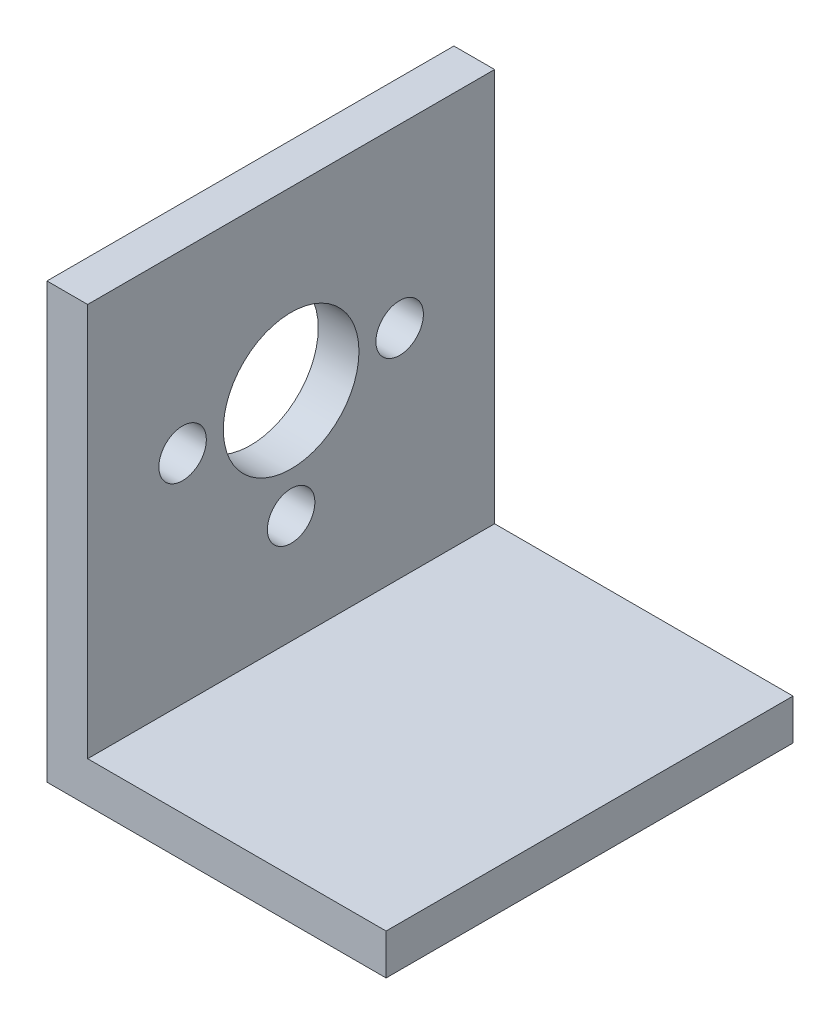
SolidWorks part; units mm, degrees
ref_plane "Front Plane" through (0, 0, 0) normal (0, 0, 1) x (1, 0, 0)
ref_plane "Top Plane" through (0, 0, 0) normal (0, 1, 0) x (1, 0, 0)
ref_plane "Right Plane" through (0, 0, 0) normal (1, 0, 0) x (0, 0, -1)
sketch "Sketch1" plane through (0, 0, 0) normal (0, 0, 1) x (1, 0, 0)
  line L0 (-7.8975, 31.3476) -> (-7.8975, 2.3476)
  line L1 (-7.8975, 2.3476) -> (14.1025, 2.3476)
  line L2 (14.1025, 2.3476) -> (14.1025, -0.6524)
  line L3 (14.1025, -0.6524) -> (-10.8975, -0.6524)
  line L4 (-10.8975, -0.6524) -> (-10.8975, 31.3476)
  line L5 (-10.8975, 31.3476) -> (-7.8975, 31.3476)
  dimension "D1" = 3
  dimension "D2" = 3
  dimension "D3" = 32
  dimension "D4" = 25
extrude "Boss-Extrude1" add sketch "Sketch1" along normal blind 30
hole_wizard "Hole for M5 300® SC Nuts (SP)1" positions "Sketch2" profile "Sketch3" hole size "M5x0.8" standard "PEM® Metric" end condition through all
sketch "Sketch2" plane through (-7.8975, 0, 0) normal (1, 0, 0) x (0, 0, -1)
  line L0 (-30, -0.6524) -> (0, -0.6524) construction
  line L1 (0, 2.3476) -> (0, 31.3476) construction
  point P0 (-15, 18.3476)
  dimension "D1" = 19
  dimension "D2" = 15
sketch "Sketch3" plane through (-7.8975, 18.3476, 15) normal (0, 1, 0) x (0, 0, -1)
  line L0 (0, 0) -> (0, 3)
  line L1 (0, 3) -> (5, 3)
  line L2 (5, 3) -> (5, 0)
  line L5 (5, 0) -> (0, 0)
  line L11 (0, -6.35) -> (0, 107.95) construction
  dimension "Thru Hole Dia." = 10
  dimension "Thru Hole Depth" = 3
hole_wizard "Hole for M5 300® SC Nuts (SP)2" positions "Sketch4" profile "Sketch5" hole size "M5x0.8" standard "PEM® Metric" end condition through all
sketch "Sketch4" plane through (-7.8975, 0, 0) normal (1, 0, 0) x (0, 0, -1)
  line L0 (-30, -0.6524) -> (0, -0.6524) construction
  line L1 (0, 2.3476) -> (0, 31.3476) construction
  circle A1 centre (-15, 18.3476) radius 5 construction
  point P0 (-7, 18.3476)
  point P2 (-23, 18.3476)
  point P4 (-15, 10.3476)
  dimension "D4" = 8
  dimension "D1" = 19
  dimension "D2" = 8
  dimension "D3" = 16
  dimension "D5" = 15
sketch "Sketch5" plane through (-7.8975, 18.3476, 7) normal (0, 1, 0) x (0, 0, -1)
  line L0 (0, 0) -> (0, 3)
  line L1 (0, 3) -> (1.75, 3)
  line L2 (1.75, 3) -> (1.75, 0)
  line L5 (1.75, 0) -> (0, 0)
  line L11 (0, -6.35) -> (0, 107.95) construction
  dimension "Thru Hole Dia." = 3.5
  dimension "Thru Hole Depth" = 3
